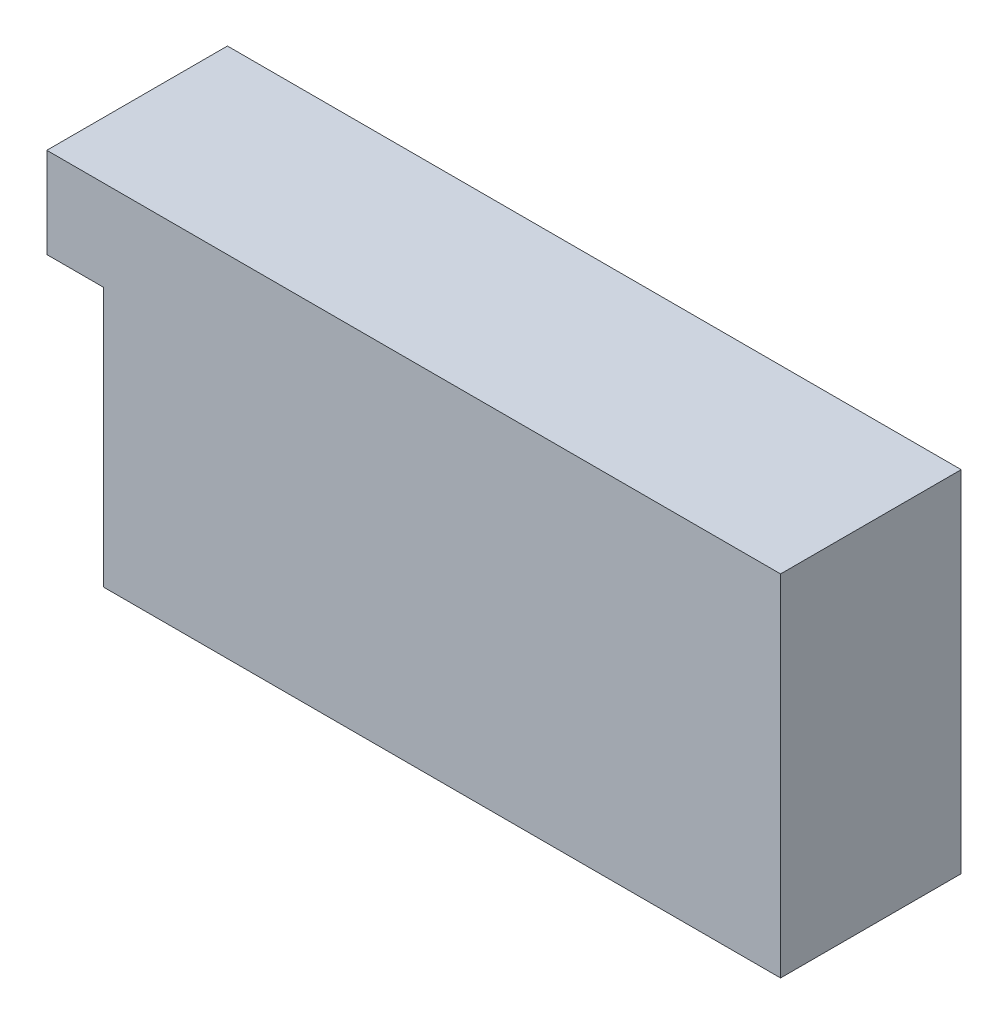
SolidWorks part; units mm, degrees
ref_plane "Front Plane" through (0, 0, 0) normal (0, 0, 1) x (1, 0, 0)
ref_plane "Top Plane" through (0, 0, 0) normal (0, 1, 0) x (1, 0, 0)
ref_plane "Right Plane" through (0, 0, 0) normal (1, 0, 0) x (0, 0, -1)
sketch "Sketch1" plane through (0, 0, 0) normal (0, 0, 1) x (1, 0, 0)
  line L1 (0, 0) -> (60, 0)
  line L2 (0, 0) -> (0, 31)
  line L3 (0, 31) -> (60, 31)
  line L4 (60, 0) -> (60, 31)
  dimension "D1" = 60
  dimension "D2" = 31
extrude "Boss-Extrude1" add sketch "Sketch1" along normal blind 16
sketch "Sketch2" plane through (0, 0, 0) normal (-1, 0, 0) x (0, 0, 1)
  line L0 (16, 31) -> (16, 0) construction
  line L1 (0, 31) -> (16, 31)
  line L2 (0, 31) -> (0, 23)
  line L3 (0, 23) -> (16, 23)
  line L4 (16, 31) -> (16, 23)
  dimension "D1" = 8
extrude "Boss-Extrude2" add sketch "Sketch2" along normal blind 5
